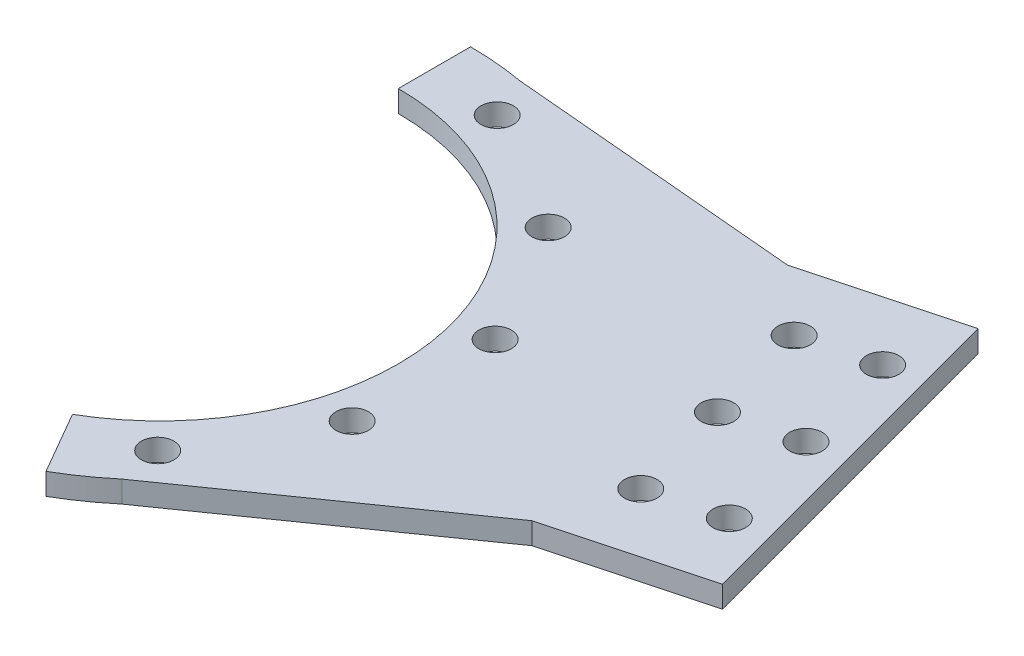
SolidWorks part; units mm, degrees
ref_plane "Front Plane" through (0, 0, 0) normal (0, 0, 1) x (1, 0, 0)
ref_plane "Top Plane" through (0, 0, 0) normal (0, 1, 0) x (1, 0, 0)
ref_plane "Right Plane" through (0, 0, 0) normal (1, 0, 0) x (0, 0, -1)
sketch "Sketch1" plane through (0, 0, 0) normal (0, 1, 0) x (1, 0, 0)
  line L0 (0, 33) -> (0, 43)
  line L1 (16.5, -28.5788) -> (21.5, -37.2391)
  arc A0 (0, 43) -> (21.5, -37.2391) centre (0, 0) cw
  arc A1 (0, 33) -> (16.5, -28.5788) centre (0, 0) cw
  dimension "D1" = 150
  dimension "D2" = 33
  dimension "D3" = 43
extrude "Boss-Extrude1" add sketch "Sketch1" along normal mid plane 3
sketch "Sketch4" plane through (0, 0, 0) normal (0, 1, 0) x (1, 0, 0)
  line L0 (0, 0) -> (53.6089, 14.3645) construction
  line L1 (68.8717, 44.336) -> (25.4051, 32.6892)
  line L2 (68.8717, 44.336) -> (81.8127, -3.9603)
  line L3 (25.4051, 32.6892) -> (38.346, -15.6071)
  line L4 (81.8127, -3.9603) -> (38.346, -15.6071)
  line L5 (31.8756, 8.541) -> (75.3422, 20.1879) construction
  line L6 (47.1384, 38.5126) -> (60.0794, -9.7837) construction
  line L7 (0, 43) -> (0, 33) construction
  arc A1 (16.5, -28.5788) -> (0, 33) centre (0, 0) ccw construction
  dimension "D1" = 75
  dimension "D2" = 78
  dimension "D3" = 50
extrude "Boss-Extrude2" add sketch "Sketch4" along normal mid plane 3
sketch "Sketch5" plane through (0, 0, 0) normal (0, 1, 0) x (1, 0, 0)
  line L0 (0, 0) -> (75.3422, 20.1879) construction
  line L1 (81.8127, -3.9603) -> (68.8717, 44.336) construction
  line L2 (0, 43) -> (48.0974, 38.7696)
  line L3 (68.8717, 44.336) -> (27.3231, 33.2031) construction
  line L4 (48.0974, 38.7696) -> (27.3231, 33.2031)
  line L5 (27.3231, 33.2031) -> (0, 43)
  line L6 (61.0384, -9.5267) -> (40.2641, -15.0932)
  line L7 (21.5, -37.2391) -> (61.0384, -9.5267)
  line L8 (40.2641, -15.0932) -> (21.5, -37.2391)
extrude "Boss-Extrude3" add sketch "Sketch5" along normal mid plane 3
sketch "Sketch2" plane through (0, 1.5, 0) normal (0, 1, 0) x (1, 0, 0)
  arc A0 (18.6469, -33.1103) -> (0, 38) centre (0, 0) ccw construction
  circle A1 centre (36.7573, 9.6387) radius 2.25
  dimension "D1" = 4.5
  dimension "D2" = 38
extrude "Cut-Extrude1" cut sketch "Sketch2" against normal through all both and the other way through all
pattern_circular "CirPattern1" count 3 every 30 about axis through (0, 0, 0) along (0, 1, 0) of "Cut-Extrude1"
sketch "Sketch6" plane through (0, 1.5, 0) normal (0, 1, 0) x (1, 0, 0)
  line L0 (64.0421, 43.0419) -> (76.9831, -5.2544) construction
  line L1 (68.8717, 44.336) -> (48.0974, 38.7696) construction
  line L2 (61.0384, -9.5267) -> (81.8127, -3.9603) construction
  line L3 (81.8127, -3.9603) -> (68.8717, 44.336) construction
  circle A0 centre (70.5126, 18.8938) radius 2.25
  dimension "D1" = 4.5
  dimension "D2" = 5
extrude "Cut-Extrude2" cut sketch "Sketch6" against normal through all both and the other way through all
pattern_linear "LPattern1" count 2 spacing 15 along (-0.2588, 0, -0.9659) count 2 spacing 10 along (-0.9659, 0, 0.2588) of "Cut-Extrude2"
pattern_linear "LPattern2" count 2 spacing 15 along (0.2588, 0, 0.9659) count 2 spacing 10 along (-0.9659, 0, 0.2588) of "Cut-Extrude2"
